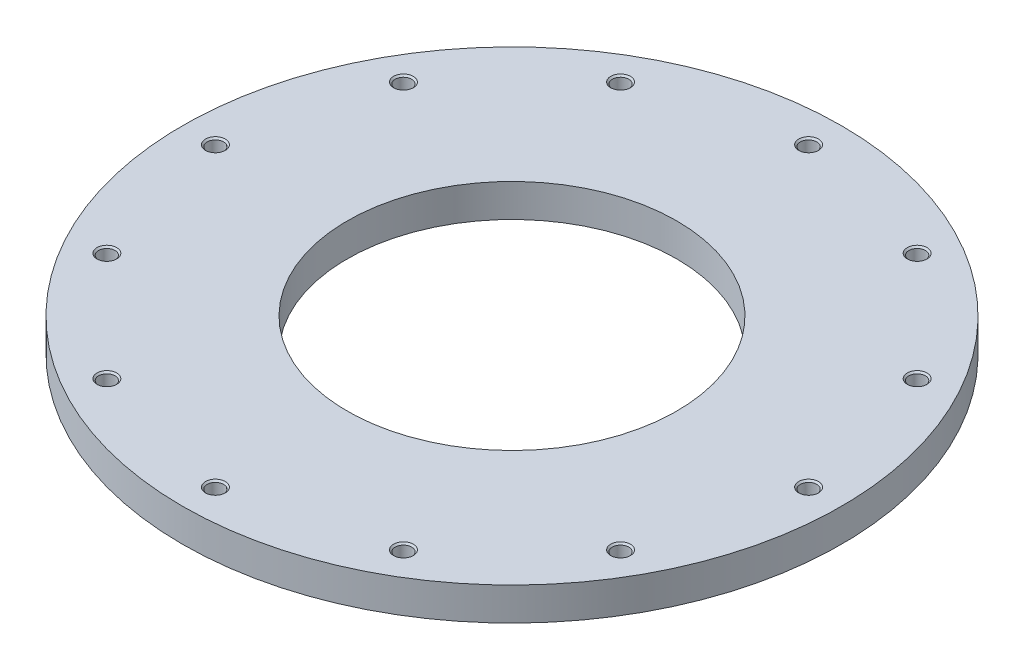
SolidWorks part; units mm, degrees
ref_plane "Front Plane" through (0, 0, 0) normal (0, 0, 1) x (1, 0, 0)
ref_plane "Top Plane" through (0, 0, 0) normal (0, 1, 0) x (1, 0, 0)
ref_plane "Right Plane" through (0, 0, 0) normal (1, 0, 0) x (0, 0, -1)
sketch "Sketch1" plane through (0, 0, 0) normal (0, 0, 1) x (1, 0, 0)
  line L0 (0, 0) -> (0, 7.5527) construction
  line L1 (-63.5, 0) -> (-127, 0)
  line L2 (-127, 0) -> (-127, -12.7)
  line L3 (-127, -12.7) -> (-63.5, -12.7)
  line L4 (-63.5, -12.7) -> (-63.5, 0)
  line L13 (-41.4381, -252.6135) -> (-25.4152, -192.8153)
  line L14 (-48.0121, -252.6135) -> (-41.4381, -252.6135)
  line L15 (-32.3308, -194.0902) -> (-48.0121, -252.6135)
  line L16 (-56.0605, -170.3605) -> (-32.3308, -194.0902)
  line L17 (-63.5, 0) -> (-63.5, -152.4)
  line L18 (-57.15, 0) -> (-63.5, 0)
  line L19 (-57.15, -152.4) -> (-57.15, 0)
  line L20 (-26.1439, -191.2968) -> (-51.5704, -165.8704)
  line L21 (-41.4381, -252.6135) -> (-25.4152, -192.8153)
  line L22 (-48.0121, -252.6135) -> (-41.4381, -252.6135)
  line L23 (-32.3308, -194.0902) -> (-48.0121, -252.6135)
  line L24 (-56.0605, -170.3605) -> (-32.3308, -194.0902)
  line L25 (-63.5, 0) -> (-63.5, -152.4)
  line L26 (-57.15, 0) -> (-63.5, 0)
  line L27 (-57.15, -152.4) -> (-57.15, 0)
  line L28 (-26.1439, -191.2968) -> (-51.5704, -165.8704)
  arc A3 (-63.5, -152.4) -> (-56.0605, -170.3605) centre (-38.1, -152.4) ccw
  arc A4 (-57.15, -152.4) -> (-51.5704, -165.8704) centre (-38.1, -152.4) ccw
  arc A5 (-25.4152, -192.8153) -> (-26.1439, -191.2968) centre (-27.94, -193.0929) ccw
  arc A6 (-63.5, -152.4) -> (-56.0605, -170.3605) centre (-38.1, -152.4) ccw
  arc A7 (-57.15, -152.4) -> (-51.5704, -165.8704) centre (-38.1, -152.4) ccw
  arc A8 (-25.4152, -192.8153) -> (-26.1439, -191.2968) centre (-27.94, -193.0929) ccw
  dimension "D1" = 12.7
  dimension "D2" = 127
  dimension "D3" = 0
revolve "Revolve1" add sketch "Sketch1" angle 360 about L0
sketch "Sketch3" plane through (0, 0, 0) normal (0, 1, 0) x (1, 0, 0)
  line L0 (0, 0) -> (114.3, 0) construction
  point P3 (99.9763, 0)
  dimension "D1" = 114.3
hole_wizard "1/4 (0.25) Diameter Hole1" positions "3DSketch3" profile "Sketch5" hole size "1/4" standard "ANSI Inch" end condition through all
sketch3d "3DSketch3"
  point P0 (114.3, 0, 0)
  point P3 (114.3, 0, 0)
  point P5 (114.3, 0, 0)
  point P7 (114.3, 0, 0)
  point P10 (114.3, 0, 0)
sketch "Sketch5" plane through (114.3, 0, 0) normal (1, 0, 0) x (0, 0, 1)
  line L0 (0, 0) -> (0, 12.7)
  line L1 (0, 12.7) -> (3.175, 12.7)
  line L2 (3.175, 12.7) -> (3.175, 0.635)
  line L3 (3.175, 0.635) -> (3.81, 0)
  line L5 (3.81, 0) -> (0, 0)
  line L6 (-3.175, 0.635) -> (-3.81, 0) construction
  line L11 (0, -6.35) -> (0, 107.95) construction
  dimension "Thru Hole Dia." = 6.35
  dimension "Thru Hole Depth" = 12.7
  dimension "Near C'Sink Dia." = 7.62
  dimension "Near C'Sink Angle" = 90
pattern_circular "CirPattern1" count 12 over 360 about axis through (0, 0, 0) along (0, 1, 0) of "1/4 (0.25) Diameter Hole1"
